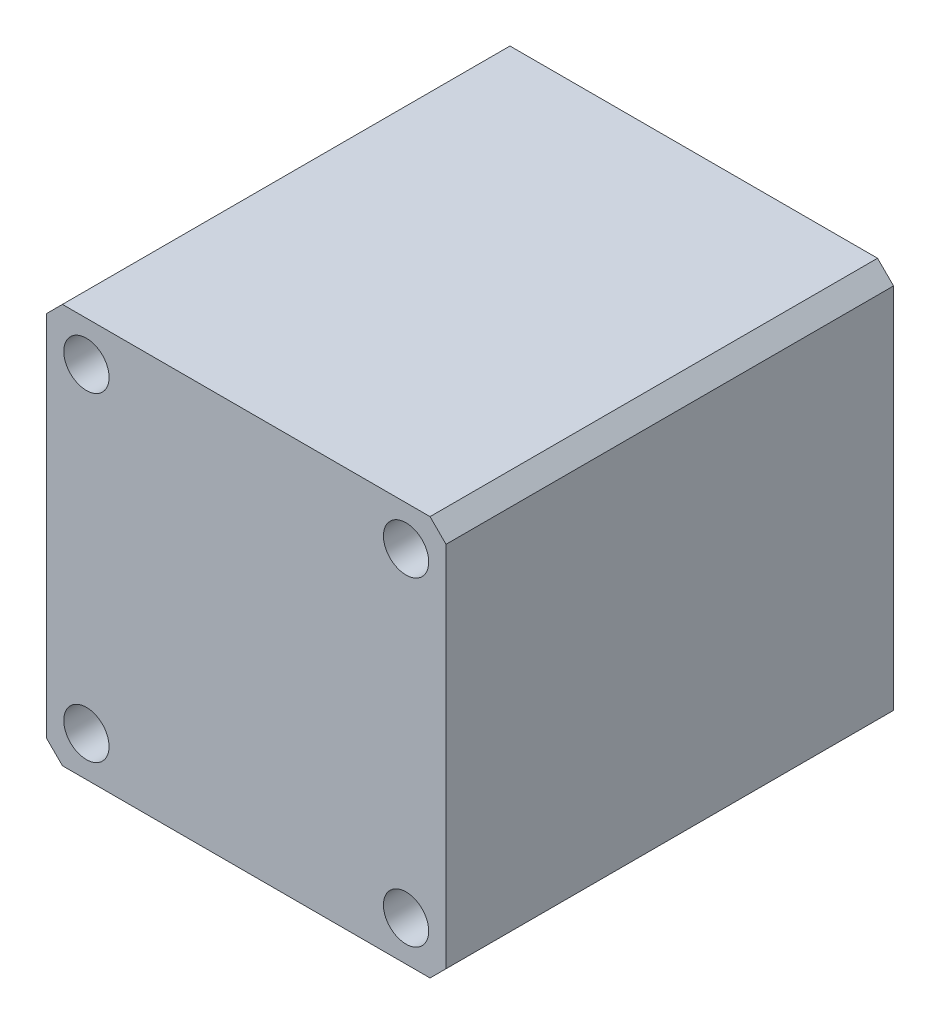
SolidWorks part; units mm, degrees
ref_plane "前视基准面" through (0, 0, 0) normal (0, 0, 1) x (1, 0, 0)
ref_plane "上视基准面" through (0, 0, 0) normal (0, 1, 0) x (1, 0, 0)
ref_plane "右视基准面" through (0, 0, 0) normal (1, 0, 0) x (0, 0, -1)
other "Configuration Table"
sketch "草图1" plane through (0, 0, 0) normal (0, 0, 1) x (1, 0, 0)
  line L1 (0, 0) -> (75, 0)
  line L2 (0, 0) -> (0, -75)
  line L3 (0, -75) -> (75, -75)
  line L4 (75, 0) -> (75, -75)
  dimension "D1" = 75
  dimension "D2" = 75
extrude "凸台-拉伸1" add sketch "草图1" along normal blind 84
chamfer "倒角1" distance 3 angle 45 4 edges at (75, -75, 42) (75, 0, 42) (0, -75, 42) (0, 0, 42)
sketch "草图2" plane through (0, 0, 84) normal (0, 0, 1) x (1, 0, 0)
  line L0 (72, 0) -> (3, 0) construction
  line L1 (0, -3) -> (0, -72) construction
  circle A0 centre (7.5, -7.5) radius 4.25
  circle A4 centre (67.5, -7.5) radius 4.25
  circle A5 centre (67.5, -67.5) radius 4.25
  circle A6 centre (7.5, -67.5) radius 4.25
  dimension "D3" = 8.5
  dimension "D1" = 7.5
  dimension "D2" = 7.5
  dimension "D4" = 2
  dimension "D5" = 2
extrude "切除-拉伸1" cut sketch "草图2" against normal through all
sketch "草图3" plane through (0, 0, 84) normal (0, 0, 1) x (1, 0, 0)
  line L0 (0, -37.5) -> (75, -37.5) construction
  line L1 (0, -3) -> (0, -72) construction
  line L2 (75, -72) -> (75, -3) construction
  line L3 (37.5, 0) -> (37.5, -75) construction
  line L4 (72, 0) -> (3, 0) construction
  line L5 (3, -75) -> (72, -75) construction
